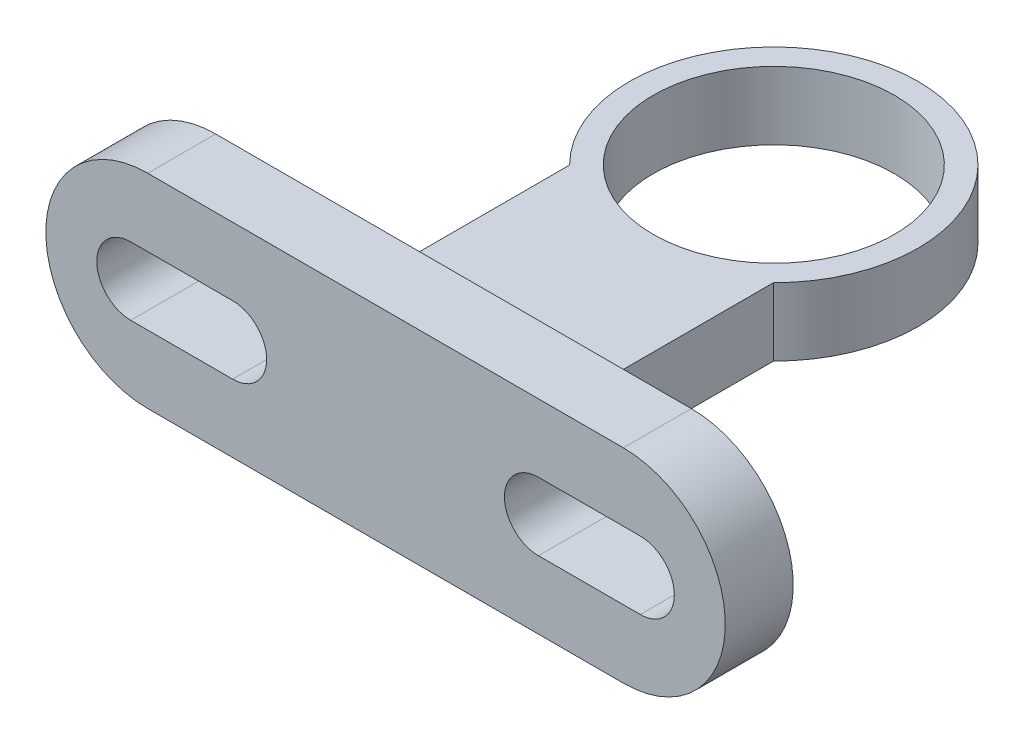
SolidWorks part; units mm, degrees
ref_plane "Front Plane" through (0, 0, 0) normal (0, 0, 1) x (1, 0, 0)
ref_plane "Top Plane" through (0, 0, 0) normal (0, 1, 0) x (1, 0, 0)
ref_plane "Right Plane" through (0, 0, 0) normal (1, 0, 0) x (0, 0, -1)
sketch "Sketch1" plane through (0, 0, 0) normal (0, 1, 0) x (1, 0, 0)
  circle A0 centre (0, 0) radius 35.5
  circle A1 centre (0, 0) radius 42.5
  dimension "D1" = 71
  dimension "D2" = 85
sketch "Sketch5" plane through (0, 0, 0) normal (0, 1, 0) x (1, 0, 0)
  line L0 (0, -42.5) -> (0, 42.5) construction
  line L1 (-30, -94.285) -> (30, -94.285)
  line L2 (30, -94.285) -> (30, -30.104)
  line L3 (-30, -94.285) -> (-30, -30.104)
  circle A0 centre (0, 0) radius 42.5 construction
  arc A1 (-30, -30.104) -> (30, -30.104) centre (0, 0) ccw
  point P6 (0, 0)
  point P10 (0, -94.285)
  dimension "D1" = 94.285
  dimension "D2" = 51.785
  dimension "D3" = 60
extrude "Boss-Extrude3" add sketch "Sketch1" along normal blind 20
extrude "Boss-Extrude4" add sketch "Sketch5" along normal blind 20
ref_plane "Plane1" through (0, 0, 94.285) normal (0, 0, 1) x (1, 0, 0)
sketch "Sketch6" plane through (0, 0, 94.285) normal (0, 0, 1) x (1, 0, 0)
  line L0 (0, 0) -> (0, 20) construction
  line L1 (-30, 20) -> (30, 20) construction
  line L2 (70, 10) -> (-70, 10) construction
  line L3 (70, -20) -> (-70, -20)
  line L4 (70, 40) -> (-70, 40)
  line L5 (-45, 10) -> (-75, 10) construction
  line L6 (-45, 0) -> (-75, 0)
  line L7 (-45, 20) -> (-75, 20)
  line L8 (45, 10) -> (75, 10) construction
  line L9 (45, 0) -> (75, 0)
  line L10 (45, 20) -> (75, 20)
  arc A0 (70, -20) -> (70, 40) centre (70, 10) ccw
  arc A1 (-70, 40) -> (-70, -20) centre (-70, 10) ccw
  arc A2 (-45, 0) -> (-45, 20) centre (-45, 10) ccw
  arc A3 (-75, 20) -> (-75, 0) centre (-75, 10) ccw
  arc A4 (45, 0) -> (45, 20) centre (45, 10) cw
  arc A5 (75, 20) -> (75, 0) centre (75, 10) cw
  point P6 (0, 10)
  point P12 (-100, 10)
  point P13 (100, 10)
  point P16 (-60, 10)
  point P21 (-35, 10)
  point P22 (-85, 10)
  point P25 (60, 10)
  dimension "D1" = 60
  dimension "D2" = 200
  dimension "D3" = 20
  dimension "D4" = 35
  dimension "D5" = 50
extrude "Boss-Extrude6" add sketch "Sketch6" along normal blind 20
